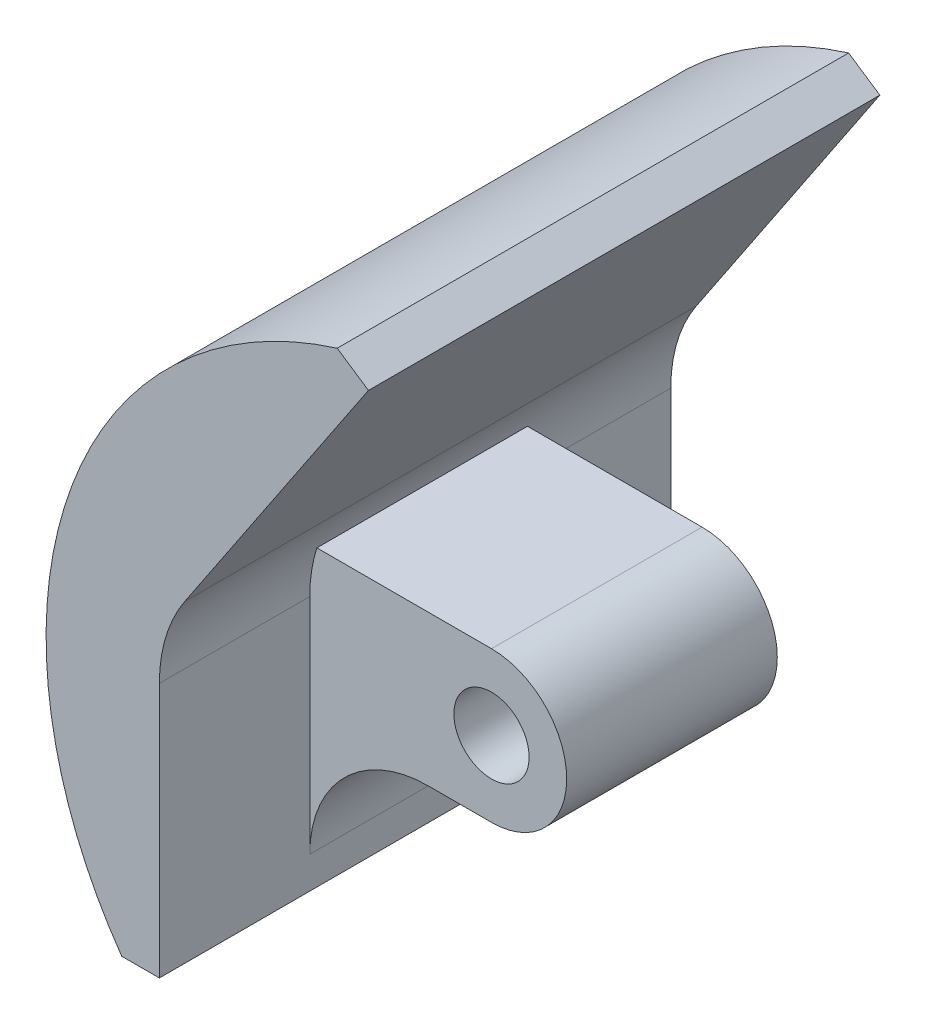
SolidWorks part; units mm, degrees
ref_plane "Front Plane" through (0, 0, 0) normal (0, 0, 1) x (1, 0, 0)
ref_plane "Top Plane" through (0, 0, 0) normal (0, 1, 0) x (1, 0, 0)
ref_plane "Right Plane" through (0, 0, 0) normal (1, 0, 0) x (0, 0, -1)
sketch "Sketch1" plane through (0, 0, 0) normal (0, 0, 1) x (1, 0, 0)
  circle A1 centre (-12.7, 137.7) radius 3.175
  circle A2 centre (-12.7, 137.7) radius 6.35
extrude "Boss-Extrude1" add sketch "Sketch1" along normal blind 17.78 contours A2 | A1
sketch "Sketch2" plane through (0, 0, 17.78) normal (0, 0, 1) x (1, 0, 0)
  line L0 (-12.7, 131.35) -> (-28.0411, 131.35)
  line L1 (-12.7, 144.05) -> (-28.0411, 144.05)
  line L2 (-28.0411, 144.05) -> (-28.0411, 131.35)
  circle A0 centre (-12.7, 137.7) radius 6.35 construction
  arc A1 (-12.7, 144.05) -> (-12.7, 131.35) centre (-12.7, 137.7) ccw
extrude "Boss-Extrude2" add sketch "Sketch2" against normal blind 17.78
sketch "Sketch3" plane through (0, 0, 17.78) normal (0, 0, 1) x (1, 0, 0)
  line L0 (-28.0411, 131.35) -> (-28.0411, 118.65)
  line L1 (-28.0411, 118.65) -> (-31.2161, 118.65)
  line L2 (-25.897, 147.2552) -> (-10.3878, 170.4398)
  line L3 (-10.3878, 170.4398) -> (-13.0268, 172.2051)
  line L4 (-28.0411, 131.35) -> (-28.0411, 140.1938)
  arc A0 (-13.0268, 172.2051) -> (-31.2161, 118.65) centre (-2.6213, 138.8046) ccw
  arc A1 (-25.897, 147.2552) -> (-28.0411, 140.1938) centre (-15.3411, 140.1938) ccw
  point P11 (-28.0411, 144.05)
  dimension "D4" = 3.175
  dimension "D5" = 12.7
  dimension "D1" = 31.75
  dimension "D2" = 12.7
  dimension "D3" = 3.175
extrude "Boss-Extrude3" add sketch "Sketch3" along normal blind 12.7 and the other way blind 30.48 contours L4 A1 L2 L3 A0 L1 L0
fillet "Fillet1" radius 10 1 edges at (-28.0411, 131.35, 8.89)
